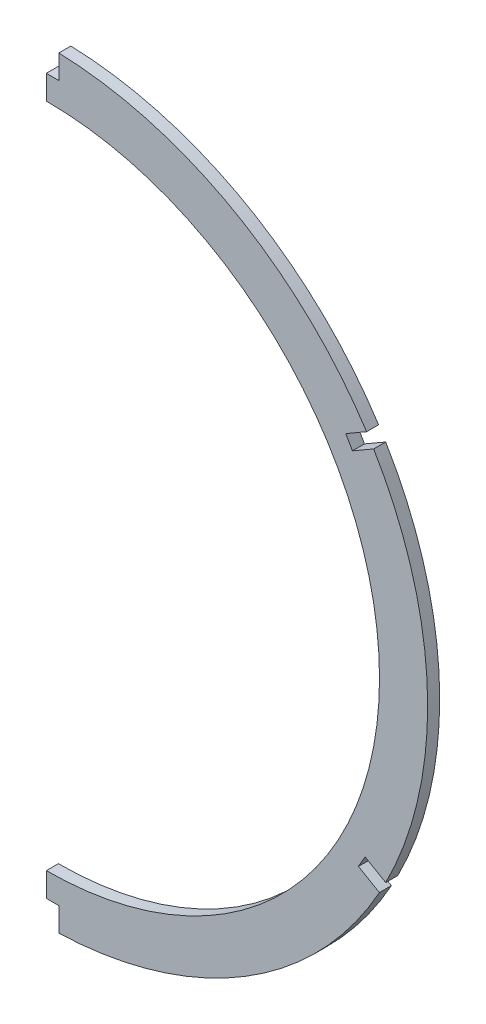
SolidWorks part; units mm, degrees
material "Plywood"
ref_plane "Front Plane" through (0, 0, 0) normal (0, 0, 1) x (1, 0, 0)
ref_plane "Top Plane" through (0, 0, 0) normal (0, 1, 0) x (1, 0, 0)
ref_plane "Right Plane" through (0, 0, 0) normal (1, 0, 0) x (0, 0, -1)
sketch "Sketch2" plane through (0, 0, 0) normal (0, 0, 1) x (1, 0, 0)
  line L0 (0, 0) -> (0, 240.9936) construction
  line L1 (-1.7839, 106.6642) -> (-1.7839, 99.822) construction
  line L2 (1.7839, 106.6642) -> (1.7839, 99.822) construction
  line L3 (-1.7839, 99.822) -> (1.7839, 99.822) construction
  line L4 (-87.7705, -42.8471) -> (-87.8712, -42.9053) construction
  line L5 (-604.1774, -338.907) -> (0, 9.8743) construction
  line L6 (-89.5483, -39.7674) -> (-83.8289, -36.4657) construction
  line L7 (-87.7705, -42.8471) -> (-82.0511, -39.5454) construction
  line L8 (-83.8289, -36.4657) -> (-82.0511, -39.5454) construction
  line L9 (604.1774, -338.907) -> (0, 9.8743) construction
  line L10 (87.7705, -42.8471) -> (82.0511, -39.5454) construction
  line L11 (87.7705, -42.8471) -> (87.8712, -42.9053) construction
  line L12 (89.5483, -39.7674) -> (83.8289, -36.4657) construction
  line L13 (83.8289, -36.4657) -> (82.0511, -39.5454) construction
  arc A0 (-7.652, 93.6463) -> (7.652, 93.6463) centre (0, 6.0782) ccw
  arc A1 (-1.7839, 106.6642) -> (-89.5483, -39.7674) centre (0, 6.0782) ccw
  arc A6 (-1.778, 93.962) -> (-7.652, 93.6463) centre (0, 6.0782) ccw
  circle A7 centre (0, 6.0782) radius 87.9018 construction
  arc A8 (0, 93.98) -> (-1.778, 93.962) centre (0, 6.0782) ccw
  arc A9 (1.778, 93.962) -> (0, 93.98) centre (0, 6.0782) ccw
  arc A10 (1.778, 93.962) -> (0, 93.98) centre (0, 6.0782) ccw construction
  arc A12 (7.652, 93.6463) -> (1.778, 93.962) centre (0, 6.0782) ccw
  arc A13 (0, 93.98) -> (-1.778, 93.962) centre (0, 6.0782) ccw construction
  arc A15 (7.652, 93.6463) -> (1.778, 93.962) centre (0, 6.0782) ccw construction
  arc A16 (-1.778, 93.962) -> (-7.652, 93.6463) centre (0, 6.0782) ccw construction
  arc A17 (0, 106.68) -> (-1.7839, 106.6642) centre (0, 6.0782) ccw
  circle A18 centre (0, 6.0782) radius 100.6018 construction
  arc A19 (1.7839, 106.6642) -> (0, 106.68) centre (0, 6.0782) ccw
  arc A20 (-87.8712, -42.9053) -> (87.8712, -42.9053) centre (0, 6.0782) ccw
  arc A21 (-89.5483, -39.7674) -> (-88.7234, -41.3442) centre (0, 6.0782) ccw
  arc A22 (-88.7234, -41.3442) -> (-87.8712, -42.9053) centre (0, 6.0782) ccw
  arc A23 (87.8712, -42.9053) -> (88.7234, -41.3442) centre (0, 6.0782) ccw
  arc A24 (89.5483, -39.7674) -> (1.7839, 106.6642) centre (0, 6.0782) ccw
  arc A25 (88.7234, -41.3442) -> (89.5483, -39.7674) centre (0, 6.0782) ccw
  point P25 (0, 99.822)
  dimension "D3" = 119.997
  dimension "D8" = 12.7
  dimension "D6" = 87.9018
  dimension "D2" = 1.7839
  dimension "D4" = 9.8743
  dimension "D5" = 3.556
  dimension "D1" = 93.98
  dimension "D7" = 5.842
  dimension "D9" = 6.604
  dimension "D10" = 3.556
extrude "Boss-Extrude1" add sketch "Sketch2" against normal blind 3.175
sketch "Sketch3" plane through (0, 0, 0) normal (1, 0, 0) x (0, 0, -1)
  line L5 (-72.4915, 152.7087) -> (76.812, 152.7087)
  line L6 (-72.4915, 152.7087) -> (-72.4915, -135.9702)
  line L7 (-72.4915, -135.9702) -> (76.812, -135.9702)
  line L8 (76.812, 152.7087) -> (76.812, -135.9702)
extrude "Cut-Extrude1" cut sketch "Sketch3" against normal through all
sketch "Sketch4" plane through (0, 0, 0) normal (0, 0, 1) x (1, 0, 0)
  line L0 (-88.1091, 62.7761) -> (-78.9966, 57.515)
  line L3 (-89.8744, 59.7185) -> (-88.1091, 62.7761)
  line L4 (0, 9.8679) -> (0, -96.8576) construction
  line L5 (0, 0) -> (0, 151.9186) construction
  line L6 (-88.9918, 61.2473) -> (-79.8792, 55.9862) construction
  line L7 (-89.8744, 59.7185) -> (-80.7619, 54.4574)
  line L8 (-80.7619, 54.4574) -> (-78.9966, 57.515)
  line L9 (-79.8792, 55.9862) -> (0, 9.8679) construction
  line L10 (0, 9.8679) -> (-60.4839, 9.8679) construction
  line L11 (-88.9918, -41.5115) -> (-79.8792, -36.2504) construction
  line L12 (-84.095, -36.646) -> (-82.3297, -39.7036)
  line L13 (-92.2228, -41.3386) -> (-84.095, -36.646)
  line L14 (-92.2228, -41.3386) -> (-90.4575, -44.3962)
  line L15 (-90.4575, -44.3962) -> (-82.3297, -39.7036)
  line L16 (-79.8792, -36.2504) -> (0, 9.8679) construction
  line L17 (3.302, -88.1737) -> (-3.302, -88.1737)
  line L18 (-3.302, -88.1737) -> (-3.302, -95.6228)
  line L19 (79.8792, -36.2504) -> (0, 9.8679) construction
  line L20 (-3.302, -95.6228) -> (3.302, -95.6228)
  line L21 (0, -95.6228) -> (0, -88.1737)
  line L22 (-3.302, 110.2958) -> (3.302, 110.2958)
  line L23 (-3.302, 110.2958) -> (-3.302, 100.33)
  line L24 (-3.302, 100.33) -> (3.302, 100.33)
  line L25 (0, 110.2958) -> (0, 100.33)
  line L26 (88.9918, -41.5115) -> (79.8792, -36.2504) construction
  line L27 (0, 9.8679) -> (60.4839, 9.8679) construction
  line L28 (79.8792, 55.9862) -> (0, 9.8679) construction
  line L29 (88.9918, 61.2473) -> (79.8792, 55.9862) construction
  line L30 (3.302, 110.2958) -> (3.302, 100.33)
  line L31 (3.302, -88.1737) -> (3.302, -95.6228)
  line L32 (90.4575, -44.3962) -> (82.3297, -39.7036)
  line L33 (92.2228, -41.3386) -> (90.4575, -44.3962)
  line L34 (92.2228, -41.3386) -> (84.095, -36.646)
  line L35 (84.095, -36.646) -> (82.3297, -39.7036)
  line L36 (80.7619, 54.4574) -> (78.9966, 57.515)
  line L37 (89.8744, 59.7185) -> (80.7619, 54.4574)
  line L38 (89.8744, 59.7185) -> (88.1091, 62.7761)
  line L39 (88.1091, 62.7761) -> (78.9966, 57.515)
  point P2 (-74.38, 52.8112)
  point P12 (-83.2124, -38.1748)
  point P19 (-77.7131, -34.9998)
  point P24 (0, -81.8237)
  point P27 (0, 93.98)
  point P49 (77.7131, -34.9998)
  point P50 (83.2124, -38.1748)
  point P51 (74.38, 52.8112)
  arc M17 (0, -94.5237) -> (0, 106.68) centre (0, 6.0782) ccw
  line M18 (0, 106.68) -> (0, 93.98)
  line M20 (0, -81.8237) -> (0, -94.5237)
  dimension "D1" = 60
  dimension "D2" = 9.8679
  dimension "D3" = 3.5306
  dimension "D4" = 85.8866
  dimension "D5" = 6.35
  dimension "D6" = 89.7354
  dimension "D7" = 6.35
  dimension "D8" = 3.5306
  dimension "D9" = 3.302
  dimension "D10" = 91.6916
  dimension "D11" = 6.35
  dimension "D12" = 84.1121
  dimension "D13" = 6.35
  dimension "D14" = 3.302
extrude "Cut-Extrude2" cut sketch "Sketch4" against normal through all contours L30 L22 L25 M17 | L30 L24 M17 M18 | L34 L35 L32 M17 | L31 L17 M20 M17 | L39 L36 L37 M17
